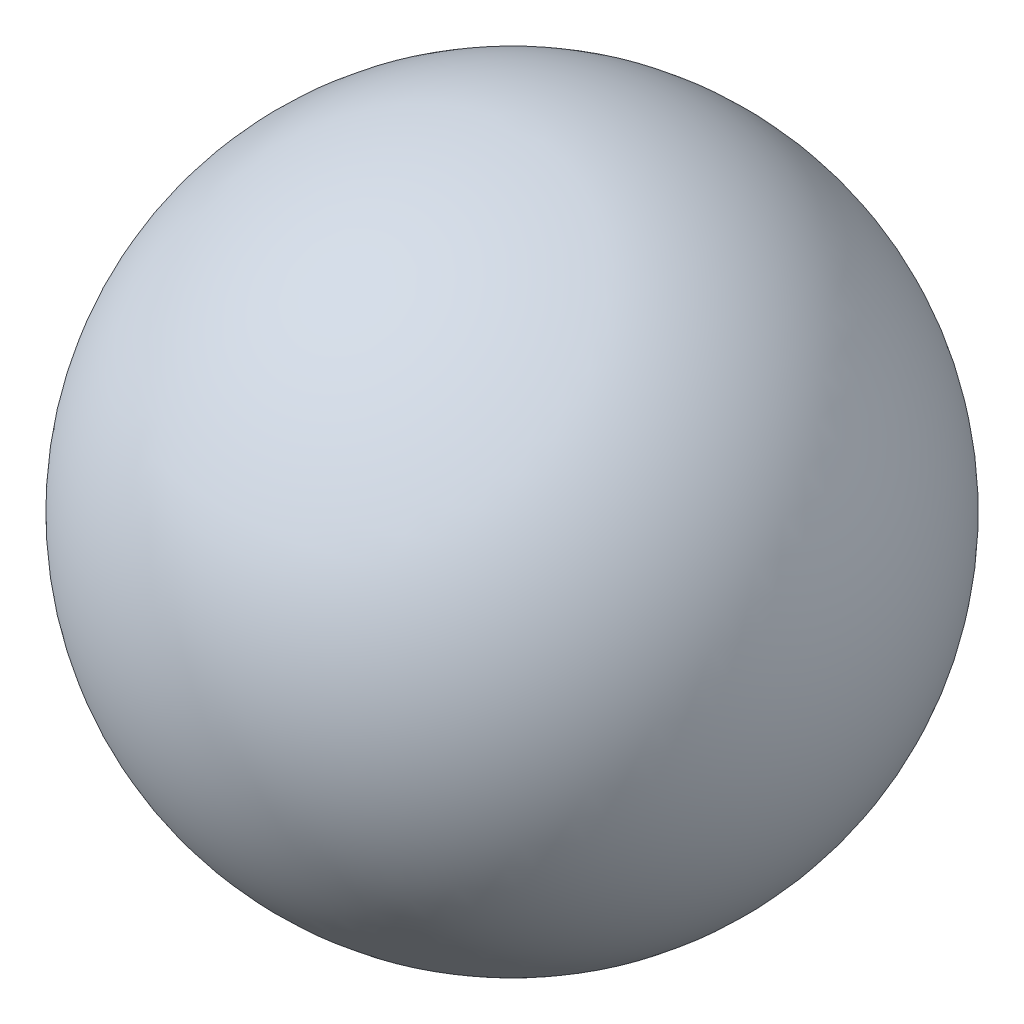
SolidWorks part; units mm, degrees
material "3.0205 (EN-AW 1200)"
ref_plane "Piano frontale" through (0, 0, 0) normal (0, 0, 1) x (1, 0, 0)
ref_plane "Piano superiore" through (0, 0, 0) normal (0, 1, 0) x (1, 0, 0)
ref_plane "Piano destro" through (0, 0, 0) normal (1, 0, 0) x (0, 0, -1)
sketch "Schizzo1" plane through (0, 0, 0) normal (1, 0, 0) x (0, 0, -1)
  line L0 (0, -22) -> (0, 22)
  arc A0 (0, 22) -> (0, -22) centre (0, 0) cw
  dimension "D1" = 22
revolve "Rivoluzione1" add sketch "Schizzo1" angle 360 about L0
